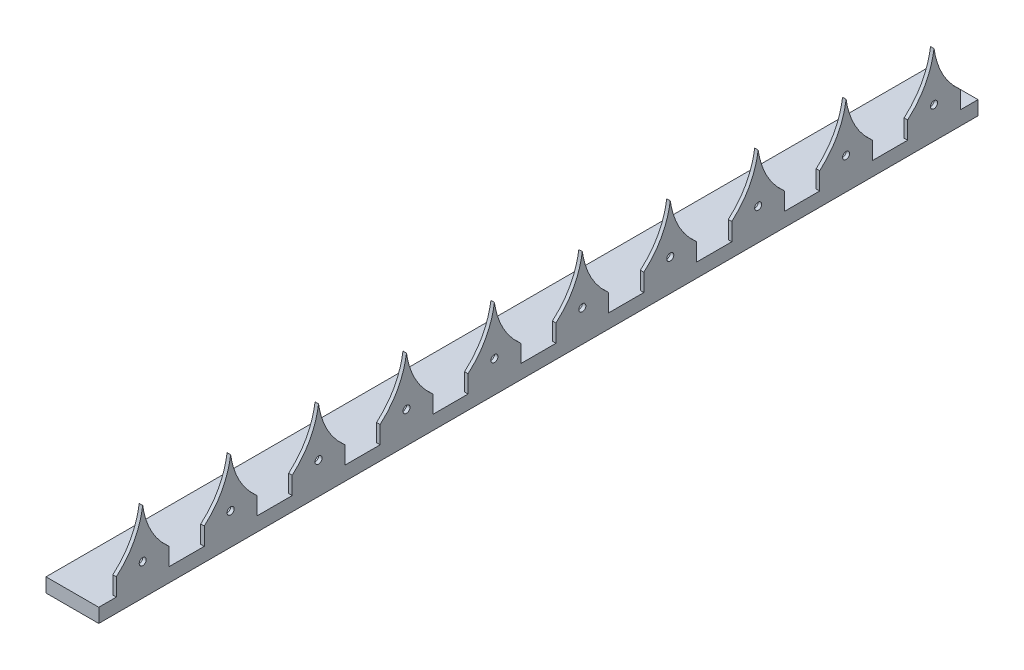
SolidWorks part; units mm, degrees
material "Plain Carbon Steel"
ref_plane "Front Plane" through (0, 0, 0) normal (0, 0, 1) x (1, 0, 0)
ref_plane "Top Plane" through (0, 0, 0) normal (0, 1, 0) x (1, 0, 0)
ref_plane "Right Plane" through (0, 0, 0) normal (1, 0, 0) x (0, 0, -1)
sketch "Sketch1" plane through (0, 0, 0) normal (0, 0, 1) x (1, 0, 0)
  line L1 (-15, -4) -> (15, -4)
  line L2 (-15, -4) -> (-15, 4)
  line L3 (-15, 4) -> (15, 4)
  line L4 (15, -4) -> (15, 4)
  line L5 (-15, -4) -> (15, 4) construction
  line L6 (-15, 4) -> (15, -4) construction
  point P0 (0, 0)
  dimension "D1" = 30
  dimension "D2" = 8
extrude "Boss-Extrude1" add sketch "Sketch1" along normal blind 50
sketch "Sketch2" plane through (15, 0, 0) normal (1, 0, 0) x (0, 0, -1)
  line L0 (-50, 4) -> (0, 4) construction
  line L1 (-40, 4) -> (-10, 4)
  line L2 (-40, 4) -> (-40, 14)
  line L3 (-40, 14) -> (-10, 14)
  line L4 (-10, 4) -> (-10, 14)
  line L5 (-40, 4) -> (-10, 14) construction
  line L6 (-40, 14) -> (-10, 4) construction
  line L7 (0, -4) -> (0, 4) construction
  line L8 (-25, 14) -> (-25, 10.7356) construction
  line L9 (-40, 14) -> (-10, 14)
  circle A0 centre (-25, 14) radius 2
  spline S0 degree 2 poles (-10, 14) (-22.5492, 24.9312) (-25, 41.6613) knots 0 0 0 1 1 1
  spline S1 degree 2 poles (-40, 14) (-27.4508, 24.9312) (-25, 41.6613) knots 0 0 0 1 1 1
  point P0 (-25, 9)
  dimension "D6" = 4
  dimension "D1" = 10
  dimension "D2" = 30
  dimension "D3" = 5
  dimension "D4" = 10
extrude "Boss-Extrude2" add sketch "Sketch2" against normal blind 2
pattern_linear "LPattern1" count 10 spacing 50 along (0, 0, -1) of "Boss-Extrude1", "Boss-Extrude2"
